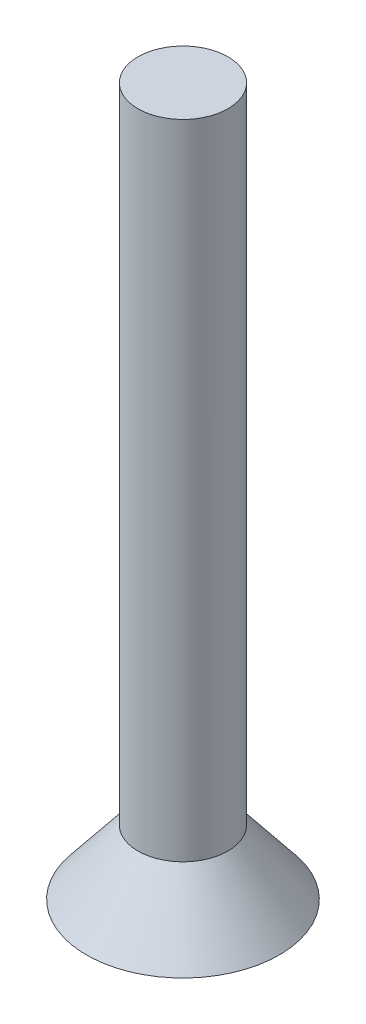
SolidWorks part; units mm, degrees
ref_plane "前视基准面" through (0, 0, 0) normal (0, 0, 1) x (1, 0, 0)
ref_plane "上视基准面" through (0, 0, 0) normal (0, 1, 0) x (1, 0, 0)
ref_plane "右视基准面" through (0, 0, 0) normal (1, 0, 0) x (0, 0, -1)
sketch "草图2" plane through (0, 0, 0) normal (0, 0, 1) x (1, 0, 0)
  line L0 (0, 0) -> (1.5, 0)
  line L1 (0, 0) -> (0, 1)
  line L2 (0, 1) -> (0.7, 1)
  line L3 (0.7, 1) -> (1.5, 0)
revolve "旋转1" add sketch "草图2" angle 360 about L1
sketch "草图3" plane through (0, 1, 0) normal (0, 1, 0) x (1, 0, 0)
  circle A0 centre (0, 0) radius 0.7
extrude "凸台-拉伸1" add sketch "草图3" along normal blind 10
sketch "草图4" plane through (0, 0, 0) normal (0, -1, 0) x (1, 0, 0)
  line L0 (0.25, -0.25) -> (0.25, -0.7651)
  line L1 (-0.7651, 0) -> (-0.7651, -0.25)
  line L2 (-0.7651, 0) -> (-0.7651, 0.25)
  line L3 (-0.7651, 0.25) -> (-0.25, 0.25)
  line L5 (-0.25, -0.25) -> (-0.7651, -0.25)
  line L6 (0, -0.7651) -> (0.25, -0.7651)
  line L7 (0, -0.7651) -> (-0.25, -0.7651)
  line L8 (-0.25, -0.7651) -> (-0.25, -0.25)
  line L10 (0.25, 0.25) -> (0.7651, 0.25)
  line L11 (0.7651, 0) -> (0.7651, 0.25)
  line L12 (0.7651, 0) -> (0.7651, -0.25)
  line L13 (0.7651, -0.25) -> (0.25, -0.25)
  line L15 (-0.25, 0.25) -> (-0.25, 0.7651)
  line L16 (0, 0.7651) -> (-0.25, 0.7651)
  line L17 (0, 0.7651) -> (0.25, 0.7651)
  line L18 (0.25, 0.7651) -> (0.25, 0.25)
  dimension "D1" = 4
extrude "切除-拉伸1" cut sketch "草图4" against normal blind 0.3
